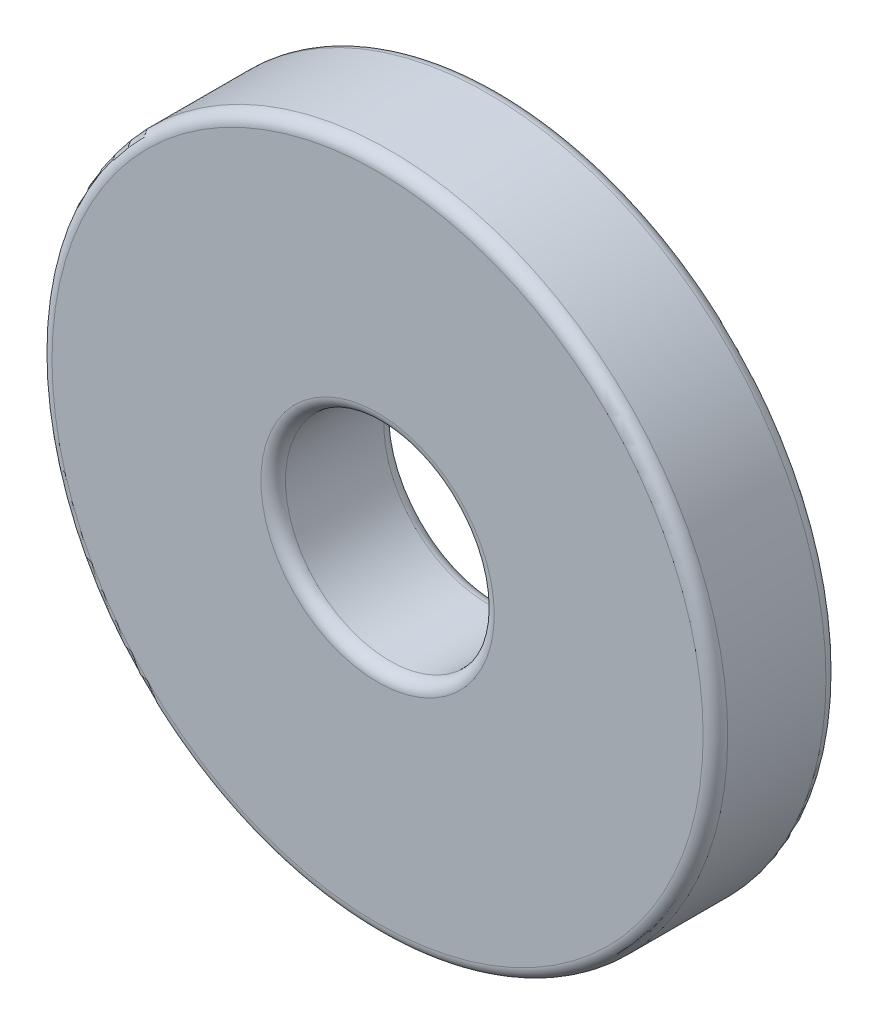
SolidWorks part; units mm, degrees
ref_plane "Front Plane" through (0, 0, 0) normal (0, 0, 1) x (1, 0, 0)
ref_plane "Top Plane" through (0, 0, 0) normal (0, 1, 0) x (1, 0, 0)
ref_plane "Right Plane" through (0, 0, 0) normal (1, 0, 0) x (0, 0, -1)
sketch "Sketch1" plane through (0, 0, 0) normal (0, 0, 1) x (1, 0, 0)
  circle A0 centre (0, 0) radius 8.5
  circle A1 centre (0, 0) radius 27.5
  dimension "D1" = 55
  dimension "D2" = 17
extrude "Boss-Extrude1" add sketch "Sketch1" along normal blind 10
fillet "Fillet1" radius 1 4 edges at (8.5, 0, 0) (8.5, 0, 10) (27.5, 0, 0) (27.5, 0, 10)
